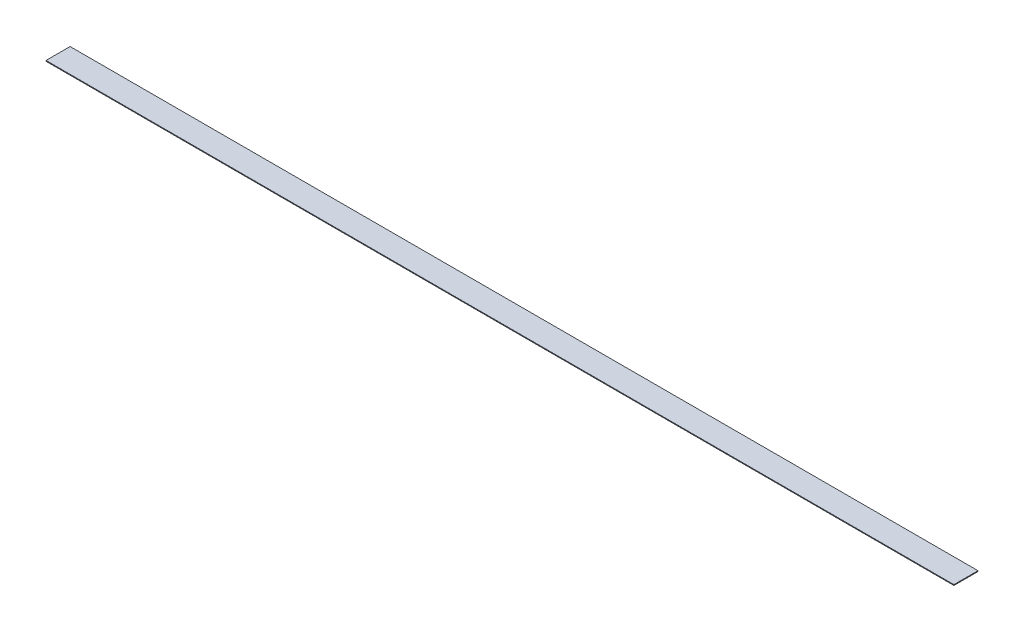
SolidWorks part; units mm, degrees
ref_plane "Front Plane" through (0, 0, 0) normal (0, 0, 1) x (1, 0, 0)
ref_plane "Top Plane" through (0, 0, 0) normal (0, 1, 0) x (1, 0, 0)
ref_plane "Right Plane" through (0, 0, 0) normal (1, 0, 0) x (0, 0, -1)
sketch "Sketch1" plane through (0, 0, 0) normal (0, 1, 0) x (1, 0, 0)
  line L1 (0, 0) -> (1914.525, 0)
  line L2 (0, 0) -> (0, 50.8)
  line L3 (0, 50.8) -> (1914.525, 50.8)
  line L4 (1914.525, 0) -> (1914.525, 50.8)
  dimension "D1" = 50.8
  dimension "D2" = 1914.525
extrude "Boss-Extrude1" add sketch "Sketch1" along normal blind 1.5875
